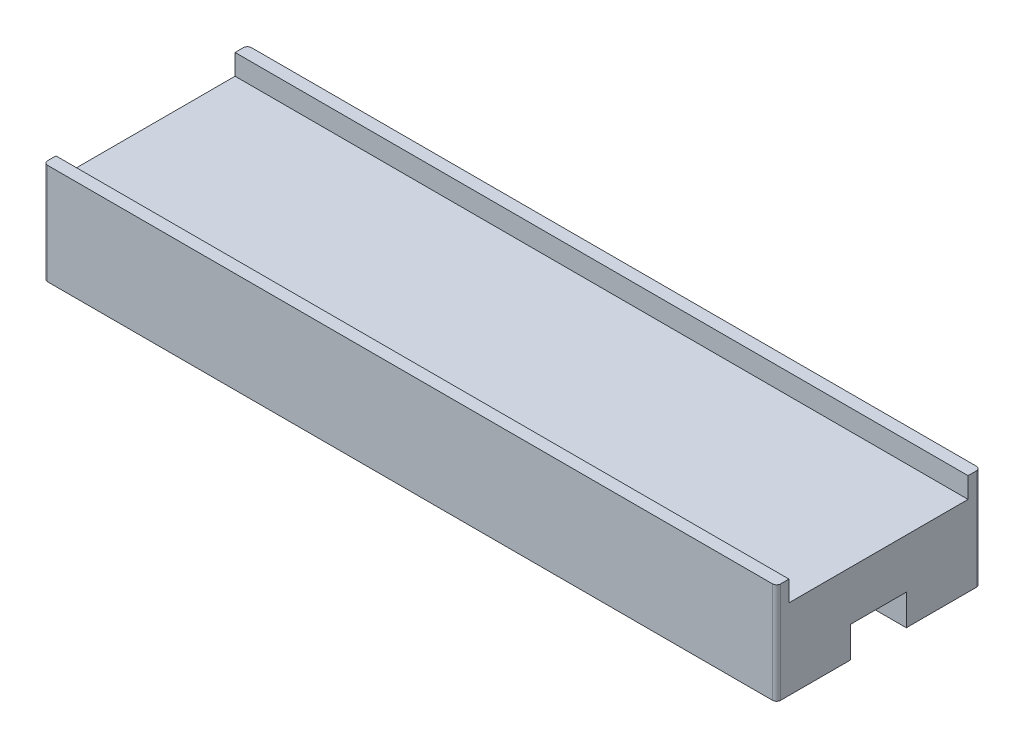
SolidWorks part; units mm, degrees
ref_plane "Plan de face" through (0, 0, 0) normal (0, 0, 1) x (1, 0, 0)
ref_plane "Plan de dessus" through (0, 0, 0) normal (0, 1, 0) x (1, 0, 0)
ref_plane "Plan de droite" through (0, 0, 0) normal (1, 0, 0) x (0, 0, -1)
sketch "Esquisse1" plane through (0, 0, 0) normal (0, 1, 0) x (1, 0, 0)
  line L1 (0, 0) -> (35.6, 0)
  line L2 (0, 0) -> (0, 9.9)
  line L3 (0, 9.9) -> (35.6, 9.9)
  line L4 (35.6, 0) -> (35.6, 9.9)
  dimension "D1" = 9.9
  dimension "D2" = 35.6
extrude "Boss.-Extru.1" add sketch "Esquisse1" along normal blind 3.9
sketch "Esquisse2" plane through (35.6, 0, 0) normal (1, 0, 0) x (0, 0, -1)
  line L0 (0, 0) -> (9.9, 0) construction
  line L1 (3.6, 0) -> (6.3, 0)
  line L2 (3.6, 0) -> (3.6, 1.5)
  line L3 (3.6, 1.5) -> (6.3, 1.5)
  line L4 (6.3, 0) -> (6.3, 1.5)
  line L5 (4.95, 3.9) -> (4.95, 0) construction
  line L6 (0, 3.9) -> (9.9, 3.9) construction
  line L7 (4.95, 1.5) -> (4.95, 0) construction
  point P12 (4.95, 0.75)
  dimension "D1" = 1.5
  dimension "D2" = 2.7
extrude "Enlèv. mat.-Extru.1" cut sketch "Esquisse2" against normal through all
sketch "Esquisse3" plane through (0, 3.9, 0) normal (0, 1, 0) x (1, 0, 0)
  line L0 (35.6, 0) -> (35.6, 9.9) construction
  line L1 (0, 0) -> (35.6, 0)
  line L2 (0, 0) -> (0, 0.6)
  line L3 (0, 0.6) -> (35.6, 0.6)
  line L4 (35.6, 0) -> (35.6, 0.6)
  line L5 (35.6, 4.95) -> (0, 4.95) construction
  line L6 (0, 9.9) -> (0, 0) construction
  line L7 (35.6, 9.9) -> (35.6, 9.3)
  line L8 (0, 9.9) -> (0, 9.3)
  line L9 (0, 9.9) -> (35.6, 9.9)
  line L10 (0, 9.3) -> (35.6, 9.3)
  dimension "D1" = 0.6
extrude "Boss.-Extru.2" add sketch "Esquisse3" along normal blind 1
fillet "Congé1" radius 0.2 4 edges at (0, 2.45, -9.9) (0, 2.45, 0) (35.6, 2.45, -9.9) (35.6, 2.45, 0)
